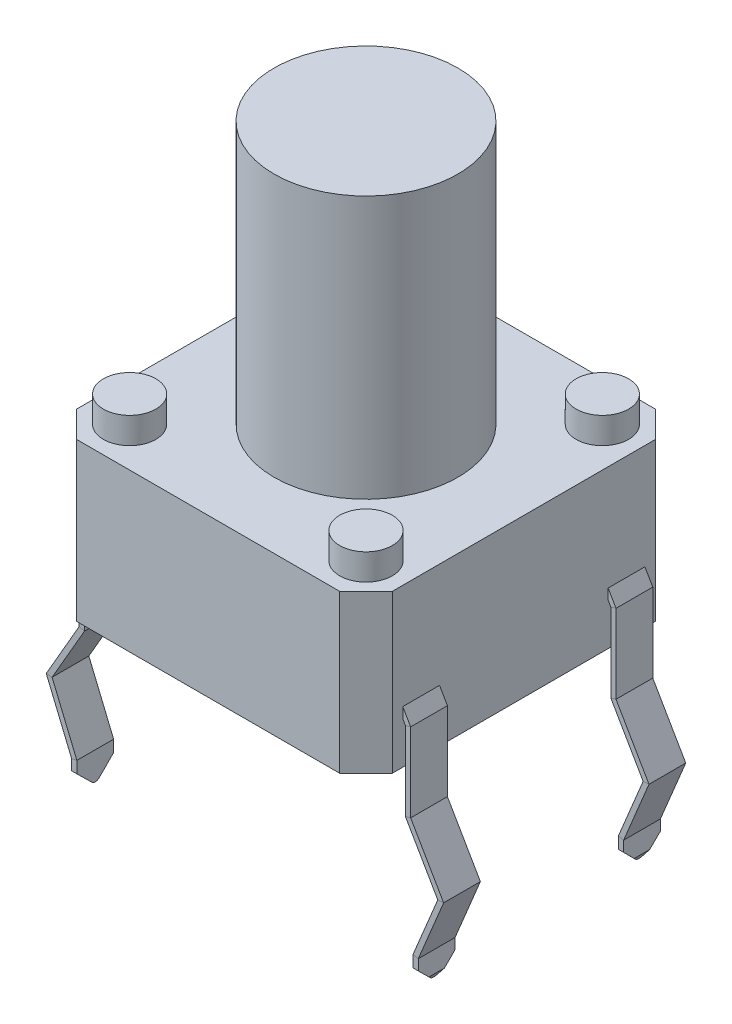
SolidWorks part; units mm, degrees
ref_plane "Front Plane" through (0, 0, 0) normal (0, 0, 1) x (1, 0, 0)
ref_plane "Top Plane" through (0, 0, 0) normal (0, 1, 0) x (1, 0, 0)
ref_plane "Right Plane" through (0, 0, 0) normal (1, 0, 0) x (0, 0, -1)
sketch "Sketch1" plane through (0, 0, 0) normal (0, 1, 0) x (1, 0, 0)
  line L1 (-3.005, -3.005) -> (3.005, -3.005)
  line L2 (-3.005, -3.005) -> (-3.005, 3.005)
  line L3 (-3.005, 3.005) -> (3.005, 3.005)
  line L4 (3.005, -3.005) -> (3.005, 3.005)
  line L5 (-3.005, -3.005) -> (3.005, 3.005) construction
  line L6 (-3.005, 3.005) -> (3.005, -3.005) construction
  point P0 (0, 0)
  dimension "D1" = 6.01
  dimension "D2" = 6.01
extrude "Boss-Extrude1" add sketch "Sketch1" along normal blind 3
chamfer "Chamfer1" distance 0.5 angle 45 4 edges at (3.005, 1.5, -3.005) (-3.005, 1.5, -3.005) (-3.005, 1.5, 3.005) (3.005, 1.5, 3.005)
sketch "Sketch3" plane through (0, 3, 0) normal (0, 1, 0) x (1, 0, 0)
  circle A0 centre (0, 0) radius 1.75
extrude "Boss-Extrude2" add sketch "Sketch3" along normal blind 5
sketch "Sketch4" plane through (0, 3, 0) normal (0, 1, 0) x (1, 0, 0)
  circle A0 centre (2.25, 2.25) radius 0.5
  circle A1 centre (2.25, -2.25) radius 0.5
  circle A2 centre (-2.25, 2.25) radius 0.5
sketch "Sketch5" plane through (0, 3, 0) normal (0, 1, 0) x (1, 0, 0)
  circle A0 centre (-2.25, -2.25) radius 0.5
extrude "Boss-Extrude6" add sketch "Sketch4" along normal blind 0.5
extrude "Boss-Extrude7" add sketch "Sketch5" along normal blind 0.5
sketch "Sketch6" plane through (-3.005, 0, 0) normal (-1, 0, 0) x (0, 0, 1)
  line L0 (-2.505, 0) -> (2.505, 0) construction
  line L1 (-2.305, 1) -> (-1.605, 1)
  line L2 (-2.305, 1) -> (-2.305, 0.8)
  line L3 (-2.305, 0.8) -> (-1.605, 0.8)
  line L4 (-1.605, 1) -> (-1.605, 0.8)
  line L5 (-2.305, 1) -> (-1.605, 0.8) construction
  line L6 (-2.305, 0.8) -> (-1.605, 1) construction
  line L7 (-2.505, 3) -> (-2.505, 0) construction
  point P0 (-1.955, 0.9)
  dimension "D1" = 0.7
  dimension "D2" = 0.2
  dimension "D3" = 1
  dimension "D4" = 0.2
sketch "Sketch7" plane through (0, 0, 0) normal (0, 0, 1) x (1, 0, 0)
  line L0 (-3.005, 0.9) -> (-3.105, 0.7268)
  line L1 (-3.105, 0.7268) -> (-3.105, -0.7732)
  line L2 (-3.105, -0.7732) -> (-3.7272, -1.8508)
  line L3 (-3.7272, -1.8508) -> (-3.25, -3)
  line L4 (-3.25, -3) -> (-3.25, -3.5)
  line L5 (2.505, 0) -> (-2.505, 0) construction
  line L6 (-3.005, 3) -> (-3.005, 0) construction
  dimension "D1" = 3.5
  dimension "D2" = 0.1
  dimension "D3" = 3.25
  dimension "D4" = 0.5
  dimension "D5" = 1.5
  dimension "D6" = 150
  dimension "D7" = 150
sweep "Sweep1" add profiles "Sketch6" path "Sketch7"
mirror "Mirror1" about plane through (0, 0, 0) normal (0, 0, 1) of "Sweep1"
mirror "Mirror2" about plane through (0, 0, 0) normal (1, 0, 0) of "Mirror1", "Sweep1"
sketch "Sketch8" plane through (0, 0, 0) normal (1, 0, 0) x (0, 0, -1)
  line L0 (-2.305, -3.2117) -> (-2.305, -3.5866)
  line L1 (-2.305, -3.01) -> (-2.305, -3.4134) construction
  line L2 (-2.305, -3.5866) -> (-1.605, -3.5866)
  line L3 (-1.605, -3.5866) -> (-1.605, -3.2117)
  line L4 (-1.605, -3.01) -> (-1.605, -3.4134) construction
  line L5 (-1.605, -3.2117) -> (-1.8817, -3.4893)
  line L6 (-2.0227, -3.4899) -> (-2.305, -3.2117)
  arc A0 (-1.8817, -3.4893) -> (-2.0227, -3.4899) centre (-1.9525, -3.4187) cw
  dimension "D1" = 0.1
extrude "Cut-Extrude1" cut sketch "Sketch8" against normal through all and the other way through all
mirror "Mirror3" about plane through (0, 0, 0) normal (0, 0, 1) of "Cut-Extrude1"
